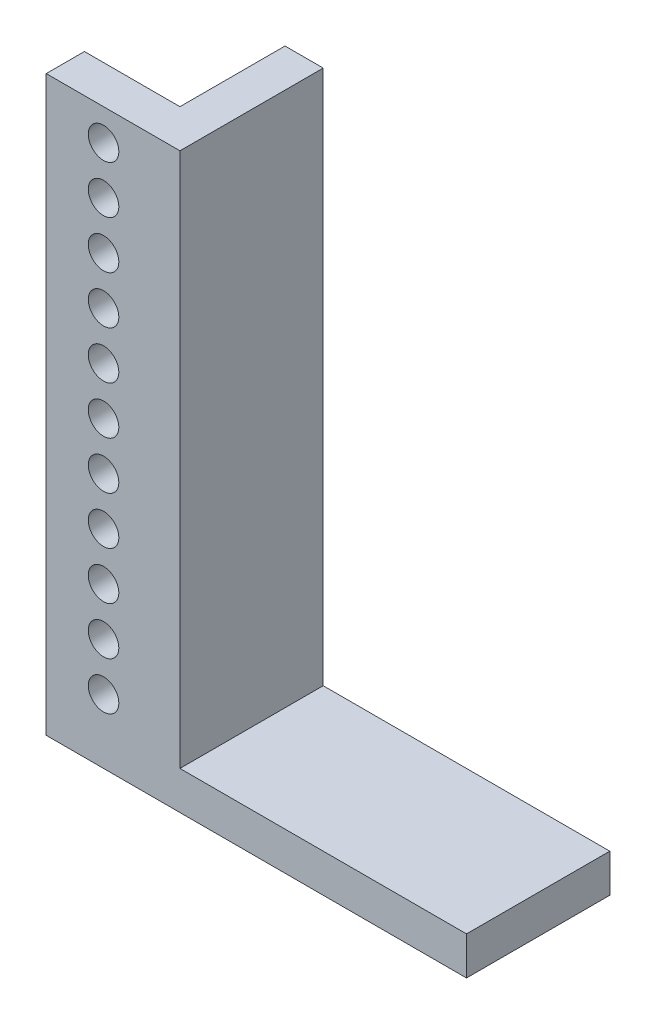
SolidWorks part; units mm, degrees
ref_plane "正面" through (0, 0, 0) normal (0, 0, 1) x (1, 0, 0)
ref_plane "平面" through (0, 0, 0) normal (0, 1, 0) x (1, 0, 0)
ref_plane "右側面" through (0, 0, 0) normal (1, 0, 0) x (0, 0, -1)
sketch "ｽｹｯﾁ1" plane through (0, 0, 0) normal (0, 0, 1) x (1, 0, 0)
  line L1 (-37.2694, 16.1798) -> (-33.2694, 16.1798)
  line L2 (-37.2694, 16.1798) -> (-37.2694, -43.8202)
  line L4 (-33.2694, 16.1798) -> (-33.2694, -39.8202)
  line L5 (-33.2694, -39.8202) -> (-3.2694, -39.8202)
  line L7 (-37.2694, -43.8202) -> (-3.2694, -43.8202)
  line L8 (-3.2694, -39.8202) -> (-3.2694, -43.8202)
  dimension "D1" = 60
  dimension "D2" = 4
  dimension "D3" = 30
  dimension "D4" = 4
extrude "ﾎﾞｽ - 押し出し1" add sketch "ｽｹｯﾁ1" along normal blind 15
sketch "ｽｹｯﾁ2" plane through (-37.2694, 0, 0) normal (-1, 0, 0) x (0, 0, 1)
  line L0 (15, -43.8202) -> (0, -43.8202) construction
  line L1 (11, 16.1798) -> (15, 16.1798)
  line L2 (11, 16.1798) -> (11, -43.8202)
  line L3 (11, -43.8202) -> (15, -43.8202)
  line L4 (15, 16.1798) -> (15, -43.8202)
  point P7 (0, 0)
  point P8 (15, 16.1798)
  dimension "D1" = 4
extrude "ﾎﾞｽ - 押し出し2" add sketch "ｽｹｯﾁ2" along normal blind 10
sketch "ｽｹｯﾁ3" plane through (0, 0, 15) normal (0, 0, 1) x (1, 0, 0)
  line L1 (-37.2694, 16.1798) -> (-37.2694, -43.8202) construction
  line L2 (-37.2694, 16.1798) -> (-37.2694, -43.8202) construction
  circle A11 centre (-41.2694, 7.9001) radius 1.6
  circle A12 centre (-41.2694, 2.9001) radius 1.6
  circle A13 centre (-41.2694, -2.0999) radius 1.6
  circle A14 centre (-41.2694, -7.0999) radius 1.6
  circle A15 centre (-41.2694, -12.0999) radius 1.6
  circle A16 centre (-41.2694, -17.0999) radius 1.6
  circle A17 centre (-41.2694, -22.0999) radius 1.6
  circle A18 centre (-41.2694, -27.0999) radius 1.6
  circle A19 centre (-41.2694, -32.0999) radius 1.6
  circle A20 centre (-41.2694, -37.0999) radius 1.6
  circle A21 centre (-41.2694, 12.9001) radius 1.6
  dimension "D1" = 3.2
  dimension "D5" = 4
  dimension "D3" = 4
  dimension "D6" = 3.2
  dimension "D7" = 4
  dimension "D8" = 4
  dimension "D9" = 4
  dimension "D10" = 4
  dimension "D11" = 4
  dimension "D12" = 3.2
  dimension "D13" = 4
  dimension "D14" = 4
  dimension "D4" = 4
  dimension "D2" = 4
extrude "ｶｯﾄ - 押し出し1" cut sketch "ｽｹｯﾁ3" against normal blind 6
